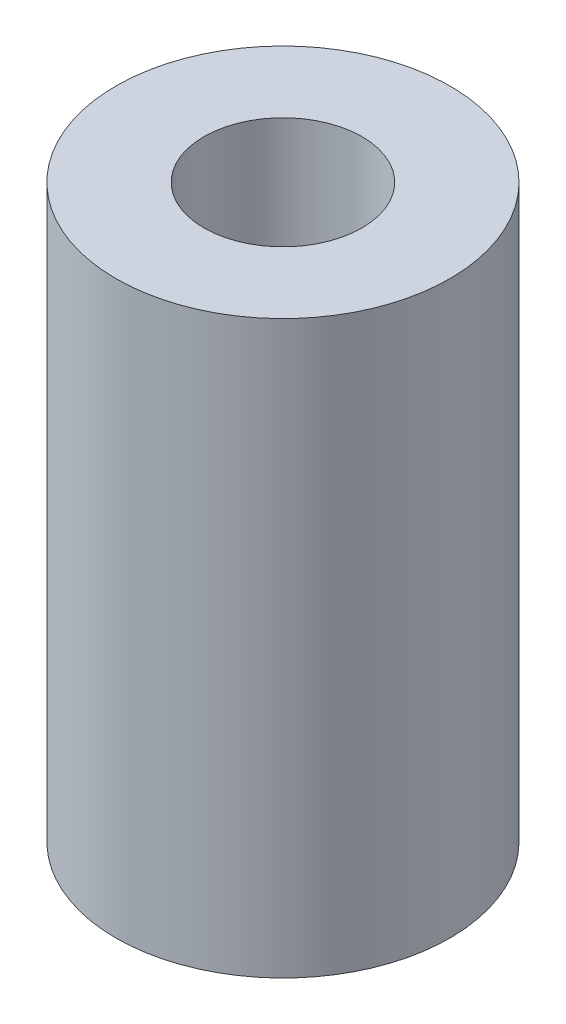
SolidWorks part; units mm, degrees
ref_plane "Front Plane" through (0, 0, 0) normal (0, 0, 1) x (1, 0, 0)
ref_plane "Top Plane" through (0, 0, 0) normal (0, 1, 0) x (1, 0, 0)
ref_plane "Right Plane" through (0, 0, 0) normal (1, 0, 0) x (0, 0, -1)
sketch "Sketch1" plane through (0, 0, 0) normal (0, 1, 0) x (1, 0, 0)
  circle A0 centre (0, 0) radius 1.8
  circle A1 centre (0, 0) radius 3.8
  dimension "D1" = 3.6
  dimension "D2" = 2
extrude "Boss-Extrude1" add sketch "Sketch1" along normal blind 13
